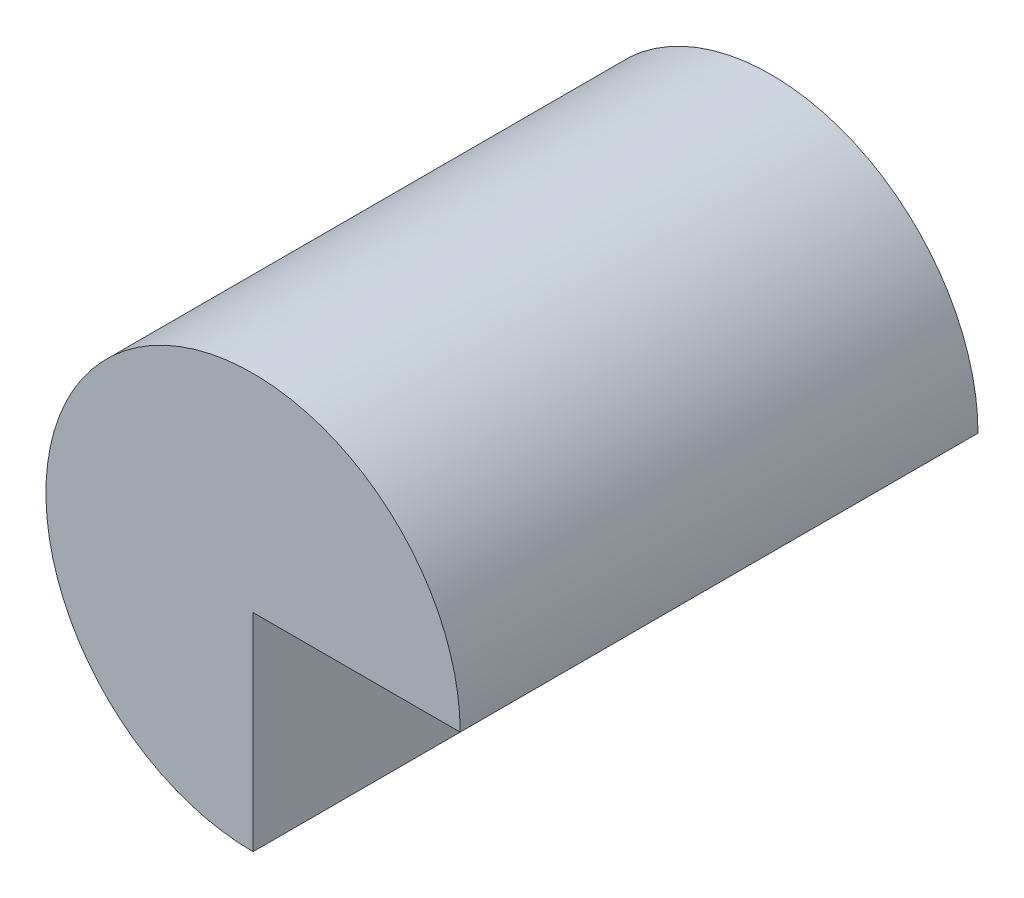
SolidWorks part; units mm, degrees
ref_plane "Front Plane" through (0, 0, 0) normal (0, 0, 1) x (1, 0, 0)
ref_plane "Top Plane" through (0, 0, 0) normal (0, 1, 0) x (1, 0, 0)
ref_plane "Right Plane" through (0, 0, 0) normal (1, 0, 0) x (0, 0, -1)
sketch "Sketch1" plane through (0, 0, 0) normal (0, 0, 1) x (1, 0, 0)
  line L0 (-10, -10) -> (-10, 0)
  line L1 (-10, 0) -> (0, 0)
  arc A0 (-10, -10) -> (0, 0) centre (-10, 0) cw
  dimension "D1" = 10
extrude "Boss-Extrude1" add sketch "Sketch1" along normal blind 25
